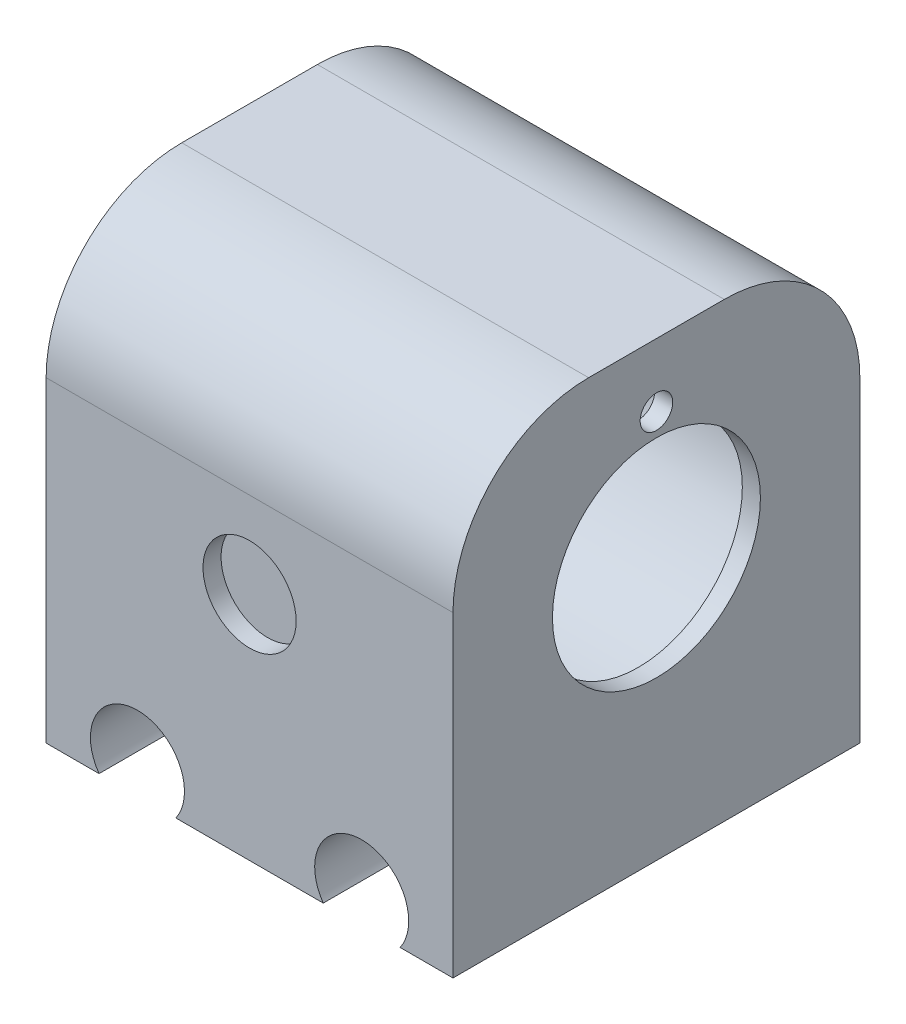
SolidWorks part; units mm, degrees
ref_plane "Front Plane" through (0, 0, 0) normal (0, 0, 1) x (1, 0, 0)
ref_plane "Top Plane" through (0, 0, 0) normal (0, 1, 0) x (1, 0, 0)
ref_plane "Right Plane" through (0, 0, 0) normal (1, 0, 0) x (0, 0, -1)
sketch "Sketch1" plane through (0, 0, 0) normal (0, 0, 1) x (1, 0, 0)
  line L1 (-14.2634, 22.0982) -> (30.7366, 22.0982)
  line L2 (-14.2634, 22.0982) -> (-14.2634, -27.9018)
  line L3 (-14.2634, -27.9018) -> (30.7366, -27.9018)
  line L4 (30.7366, 22.0982) -> (30.7366, -27.9018)
  dimension "D1" = 50
  dimension "D2" = 45
extrude "Boss-Extrude1" add sketch "Sketch1" along normal blind 45
sketch "Sketch2" plane through (0, 0, 45) normal (0, 0, 1) x (1, 0, 0)
  line L0 (-14.2634, -27.9018) -> (30.7366, -27.9018) construction
  line L1 (-14.2634, 22.0982) -> (-14.2634, -27.9018) construction
  circle A0 centre (-4.1634, -24.9018) radius 5.2
  circle A1 centre (20.6366, -24.9018) radius 5.2
  dimension "D1" = 3
  dimension "D3" = 10.1
  dimension "D2" = 2
extrude "Cut-Extrude1" cut sketch "Sketch2" against normal blind 45
sketch "Sketch9" plane through (0, 0, 45) normal (0, 0, 1) x (1, 0, 0)
  line L0 (8.2366, 22.0982) -> (8.2366, -2.4018) construction
  line L1 (30.7366, 22.0982) -> (-14.2634, 22.0982) construction
  circle A0 centre (8.2366, -2.4018) radius 5.15
  dimension "D1" = 24.5
extrude "Cut-Extrude6" cut sketch "Sketch9" against normal blind 2
sketch "Sketch10" plane through (0, 0, 0) normal (0, 0, -1) x (-1, 0, 0)
  line L0 (-8.2366, 22.0982) -> (-8.2366, -2.4018) construction
  line L1 (-30.7366, 22.0982) -> (14.2634, 22.0982) construction
  circle A0 centre (-8.2366, -2.4018) radius 5.15
  dimension "D1" = 24.5
extrude "Cut-Extrude7" cut sketch "Sketch10" against normal blind 2
sketch "Sketch12" plane through (-14.2634, 0, 0) normal (-1, 0, 0) x (0, 0, 1)
  line L0 (22.5, 22.0982) -> (22.5, -7.2504) construction
  line L1 (45, 22.0982) -> (0, 22.0982) construction
  line L2 (0, -16.4263) -> (45, -16.4263) construction
  line L3 (0, 22.0982) -> (0, -27.9018) construction
  line L4 (45, 22.0982) -> (45, -27.9018) construction
  circle A0 centre (22.5, 1.0982) radius 18.375
  dimension "D1" = 36.75
extrude "Cut-Extrude8" cut sketch "Sketch12" against normal blind 45
sketch "Sketch13" plane through (-14.2634, 0, 0) normal (-1, 0, 0) x (0, 0, 1)
  line L0 (45, 22.0982) -> (45, -27.9018) construction
  line L1 (0, 22.0982) -> (45, 22.0982)
  line L2 (0, 22.0982) -> (0, 15.4307)
  line L3 (0, 15.4307) -> (45, 15.4307)
  line L4 (45, 22.0982) -> (45, 15.4307)
extrude "Cut-Extrude9" cut sketch "Sketch13" against normal blind 46
sketch "Sketch14" plane through (-14.2634, 0, 0) normal (-1, 0, 0) x (0, 0, 1)
  line L1 (0, 15.4307) -> (45, 15.4307)
  line L2 (0, 15.4307) -> (0, 22.0982)
  line L3 (0, 22.0982) -> (45, 22.0982)
  line L4 (45, 15.4307) -> (45, 22.0982)
  dimension "D1" = 45
extrude "Boss-Extrude2" add sketch "Sketch14" against normal blind 45
sketch "Sketch15" plane through (-14.2634, 0, 0) normal (-1, 0, 0) x (0, 0, 1)
  circle A0 centre (22.5, 1.0982) radius 18.375
extrude "Cut-Extrude10" cut sketch "Sketch15" against normal blind 45
fillet "Fillet1" radius 15 2 edges at (8.2366, 22.0982, 45) (8.2366, 22.0982, 0)
sketch "Sketch16" plane through (30.7366, 0, 0) normal (1, 0, 0) x (0, 0, -1)
  circle A0 centre (-22.5, 1.0982) radius 18.375
extrude "Boss-Extrude3" add sketch "Sketch16" against normal blind 2
sketch "Sketch17" plane through (30.7366, 0, 0) normal (1, 0, 0) x (0, 0, -1)
  circle A0 centre (-22.5, 1.0982) radius 11.5
extrude "Cut-Extrude11" cut sketch "Sketch17" against normal blind 2
sketch "Sketch18" plane through (30.7366, 0, 0) normal (1, 0, 0) x (0, 0, -1)
  circle A0 centre (-22.5, 1.0982) radius 14 construction
  circle A1 centre (-22.5, 15.0982) radius 1.8
extrude "Cut-Extrude12" cut sketch "Sketch18" against normal blind 2
